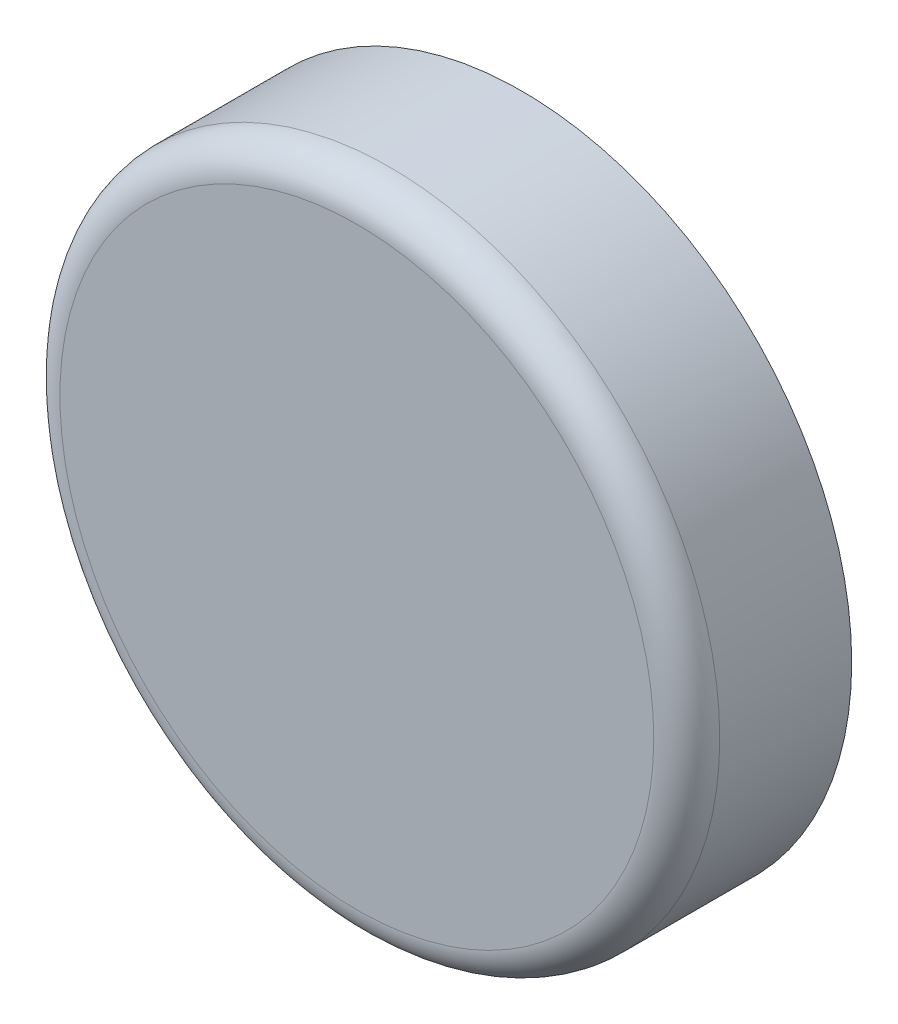
SolidWorks part; units mm, degrees
ref_plane "Front Plane" through (0, 0, 0) normal (0, 0, 1) x (1, 0, 0)
ref_plane "Top Plane" through (0, 0, 0) normal (0, 1, 0) x (1, 0, 0)
ref_plane "Right Plane" through (0, 0, 0) normal (1, 0, 0) x (0, 0, -1)
sketch "Sketch1" plane through (0, 0, 0) normal (0, 0, 1) x (1, 0, 0)
  circle A0 centre (-11.2277, 10.6772) radius 10
extrude "Boss-Extrude1" add sketch "Sketch1" along normal blind 5
fillet "Fillet1" radius 1 1 edges at (-1.2277, 10.6772, 5)
